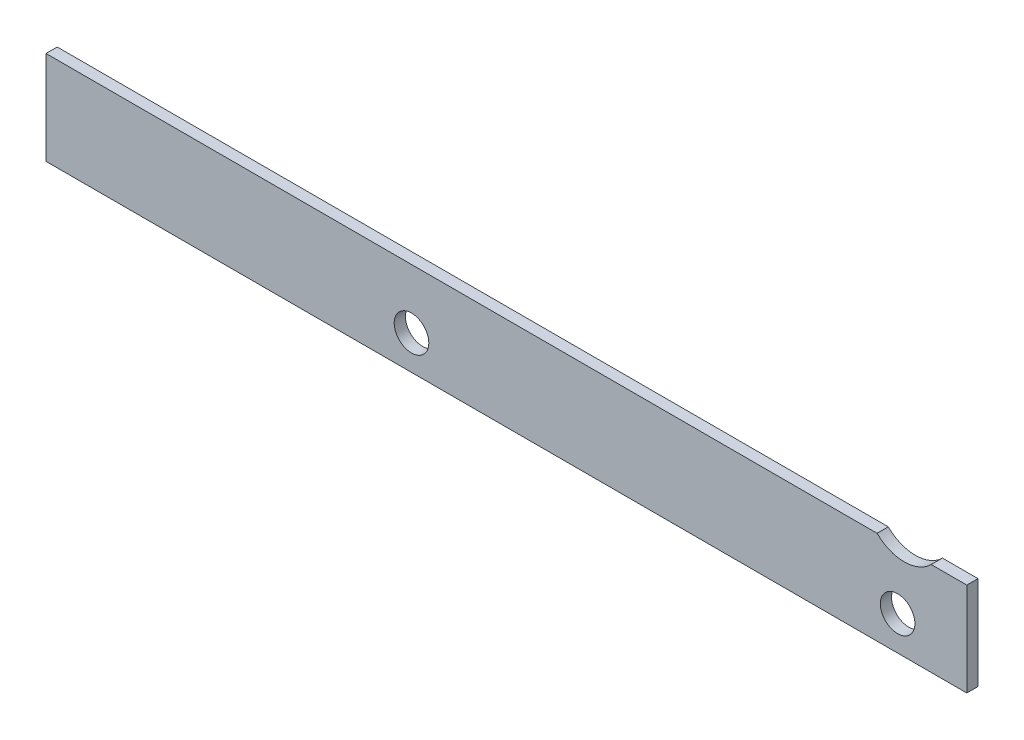
SolidWorks part; units mm, degrees
ref_plane "Alzado" through (0, 0, 0) normal (0, 0, 1) x (1, 0, 0)
ref_plane "Planta" through (0, 0, 0) normal (0, 1, 0) x (1, 0, 0)
ref_plane "Vista lateral" through (0, 0, 0) normal (1, 0, 0) x (0, 0, -1)
sketch "Croquis1" plane through (0, 0, 0) normal (0, 0, 1) x (1, 0, 0)
  line L0 (0, 0) -> (985, 0)
  line L1 (985, 0) -> (985, 100)
  line L2 (985, 100) -> (946.9524, 100)
  line L3 (0, 100) -> (0, 0)
  line L4 (918, 0) -> (918, 129) construction
  line L5 (918, 129) -> (985, 129) construction
  line L6 (985, 129) -> (985, 100) construction
  line L7 (889.0476, 100) -> (0, 100)
  arc A1 (889.0476, 100) -> (946.9524, 100) centre (918, 129) ccw
  dimension "D1" = 985
  dimension "D2" = 100
  dimension "D3" = 129
  dimension "D4" = 67
extrude "Saliente-Extruir1" add sketch "Croquis1" along normal blind 12
sketch "Croquis2" plane through (0, 0, 12) normal (0, 0, 1) x (1, 0, 0)
  line L0 (985, 48.4068) -> (985, 36.5) construction
  line L1 (985, 0) -> (985, 100) construction
  line L2 (985, 36.5) -> (911, 36.5) construction
  line L3 (911, 36.5) -> (911, 0) construction
  line L4 (0, 0) -> (985, 0) construction
  circle A0 centre (911, 36.5) radius 18.5
  dimension "D1" = 36.5
  dimension "D2" = 74
extrude "Cortar-Extruir1" cut sketch "Croquis2" against normal through all
sketch "Croquis3" plane through (0, 0, 12) normal (0, 0, 1) x (1, 0, 0)
  line L0 (391, 0) -> (391, 36.5) construction
  line L1 (0, 0) -> (985, 0) construction
  line L2 (391, 36.5) -> (0, 36.5) construction
  line L4 (0, 100) -> (0, 0) construction
  circle A0 centre (391, 36.5) radius 18.5
  dimension "D1" = 391
  dimension "D2" = 36.5
extrude "Cortar-Extruir2" cut sketch "Croquis3" against normal through all
